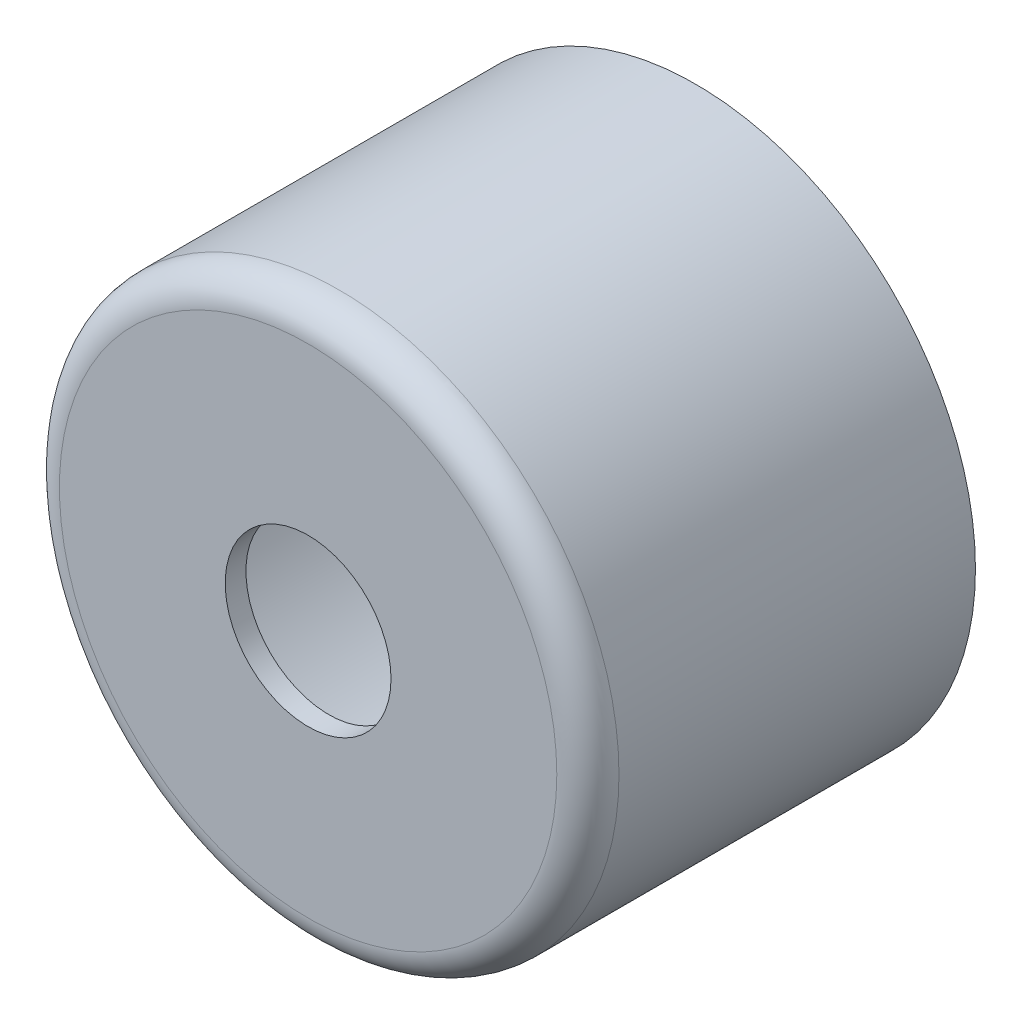
SolidWorks part; units mm, degrees
ref_plane "Plan de face" through (0, 0, 0) normal (0, 0, 1) x (1, 0, 0)
ref_plane "Plan de dessus" through (0, 0, 0) normal (0, 1, 0) x (1, 0, 0)
ref_plane "Plan de droite" through (0, 0, 0) normal (1, 0, 0) x (0, 0, -1)
sketch "Esquisse1" plane through (0, 0, 0) normal (0, 0, 1) x (1, 0, 0)
  circle A0 centre (0, 0) radius 13.5
extrude "Extrusion1" add sketch "Esquisse1" along normal blind 18.7
fillet "Congé1" radius 1.5 1 edges at (13.5, 0, 18.7)
shell "Coque1" thickness 1
sketch "Esquisse2" plane through (0, 0, 18.7) normal (0, 0, 1) x (1, 0, 0)
  circle A0 centre (0, 0) radius 4
extrude "Enlèv. mat.-Extru.1" cut sketch "Esquisse2" against normal through all
